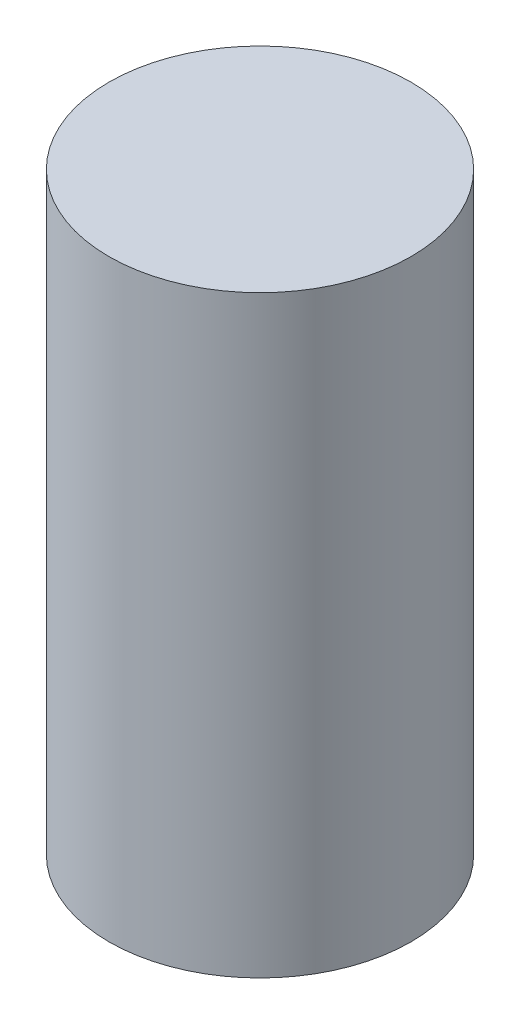
SolidWorks part; units mm, degrees
ref_plane "Front Plane" through (0, 0, 0) normal (0, 0, 1) x (1, 0, 0)
ref_plane "Top Plane" through (0, 0, 0) normal (0, 1, 0) x (1, 0, 0)
ref_plane "Right Plane" through (0, 0, 0) normal (1, 0, 0) x (0, 0, -1)
sketch "Sketch1" plane through (0, 0, 0) normal (0, 1, 0) x (1, 0, 0)
  circle A0 centre (0, 0) radius 280
  dimension "D1" = 560
extrude "Boss-Extrude1" add sketch "Sketch1" along normal blind 1100
